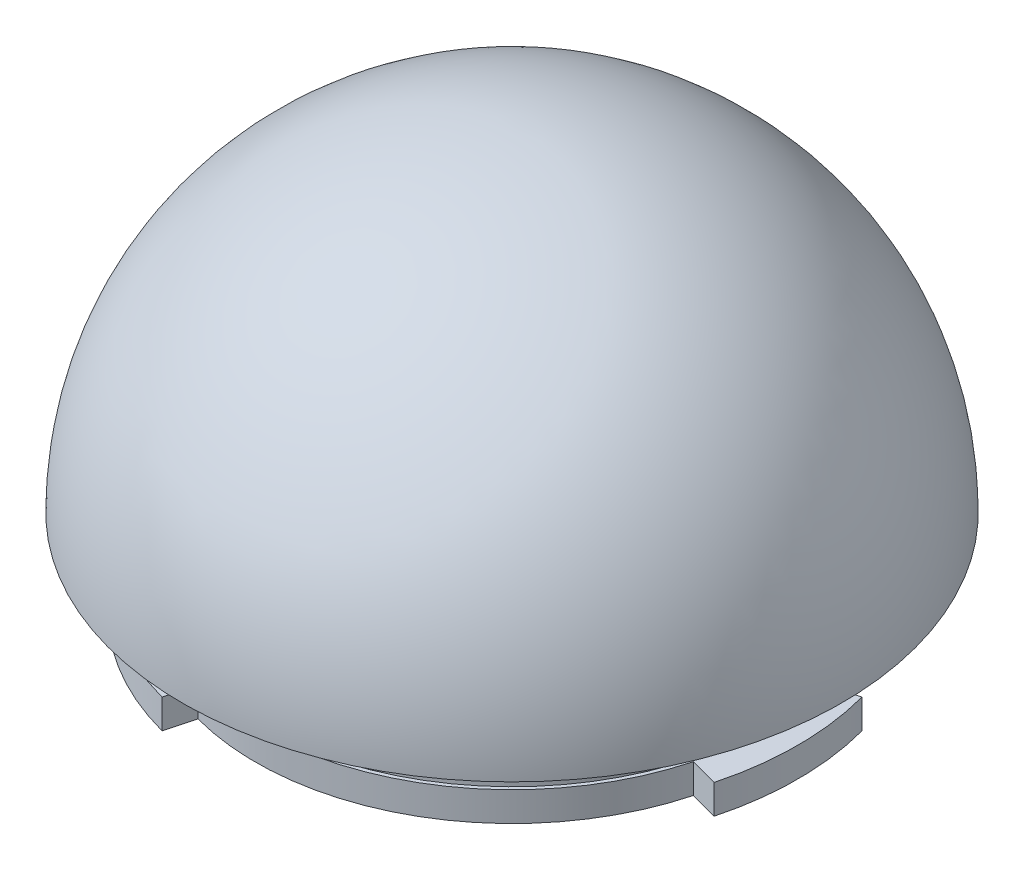
SolidWorks part; units mm, degrees
material "ABS"
ref_plane "Front Plane" through (0, 0, 0) normal (0, 0, 1) x (1, 0, 0)
ref_plane "Top Plane" through (0, 0, 0) normal (0, 1, 0) x (1, 0, 0)
ref_plane "Right Plane" through (0, 0, 0) normal (1, 0, 0) x (0, 0, -1)
sketch "Sketch1" plane through (0, 0, 0) normal (0, 1, 0) x (1, 0, 0)
  line L0 (1.2205, 44.9834) -> (-1.2205, -44.9834)
  arc A0 (-1.2205, -44.9834) -> (1.2205, 44.9834) centre (0, 0) ccw
  dimension "D1" = 90
revolve "Revolve1" add sketch "Sketch1" angle 180 about L0
sketch "Sketch2" plane through (0, 0, 0) normal (0, -1, 0) x (1, 0, 0)
  line L0 (39.9846, 1.1115) -> (-39.9846, -1.1115)
  arc A0 (39.9846, 1.1115) -> (-39.9846, -1.1115) centre (0, 0) ccw
  dimension "D1" = 80
revolve "Cut-Revolve1" cut sketch "Sketch2" angle 360 about L0
sketch "Sketch4" plane through (0, 0, 0) normal (0, -1, 0) x (1, 0, 0)
  circle A0 centre (0, 0) radius 41.295
extrude "Boss-Extrude1" add sketch "Sketch4" against normal blind 7
sketch "Sketch5" plane through (0, 0, 0) normal (0, -1, 0) x (1, 0, 0)
  circle A0 centre (0, 0) radius 34.5
  dimension "D1" = 69
extrude "Boss-Extrude2" add sketch "Sketch5" along normal blind 12
sketch "Sketch6" plane through (0, -12, 0) normal (0, -1, 0) x (1, 0, 0)
  circle A0 centre (0, 0) radius 39
  dimension "D1" = 78
extrude "Boss-Extrude4" add sketch "Sketch6" against normal blind 4
sketch "Sketch7" plane through (0, -12, 0) normal (0, -1, 0) x (1, 0, 0)
  circle A0 centre (0, 0) radius 30
  dimension "D1" = 60
extrude "Cut-Extrude1" cut sketch "Sketch7" against normal blind 24
sketch "Sketch8" plane through (0, -12, 0) normal (0, -1, 0) x (1, 0, 0)
  line L5 (-10.3528, 38.637) -> (-9.0587, 33.8074)
  line L6 (-28.2843, 28.2843) -> (-24.7487, 24.7487)
  line L9 (-9.0587, -33.8074) -> (-10.3528, -38.637)
  line L10 (-28.2843, -28.2843) -> (-24.7487, -24.7487)
  line L11 (38.637, -10.3528) -> (33.6984, -9.0294)
  line L12 (38.4748, 10.4313) -> (38.637, 10.3528)
  line L13 (38.637, 10.3528) -> (33.8074, 9.0587)
  arc A0 (-28.2843, 28.2843) -> (-28.2843, -28.2843) centre (0, 0) ccw
  arc A1 (-24.7487, 24.7487) -> (-24.7487, -24.7487) centre (0, 0) ccw
  arc A2 (33.8074, 9.0587) -> (-9.0587, 33.8074) centre (0, 0) ccw
  arc A3 (38.637, 10.3528) -> (-10.3528, 38.637) centre (0, 0) ccw
  arc A4 (-9.0587, -33.8074) -> (33.8074, -9.0587) centre (0, 0) ccw
  arc A5 (-10.3528, -38.637) -> (38.637, -10.3528) centre (0, 0) ccw
  circle M4 centre (0, 0) radius 39
  dimension "D1" = 80
  dimension "D2" = 70
  dimension "D3" = 30
  dimension "D4" = 30
  dimension "D5" = 30
  dimension "D6" = 90
  dimension "D7" = 90
  dimension "D8" = 90
  dimension "D9" = 5
extrude "Cut-Extrude2" cut sketch "Sketch8" against normal blind 10 contours A2 L13 L5 M4 | A4 L9 L11 M4 | A1 L6 L10 M4
